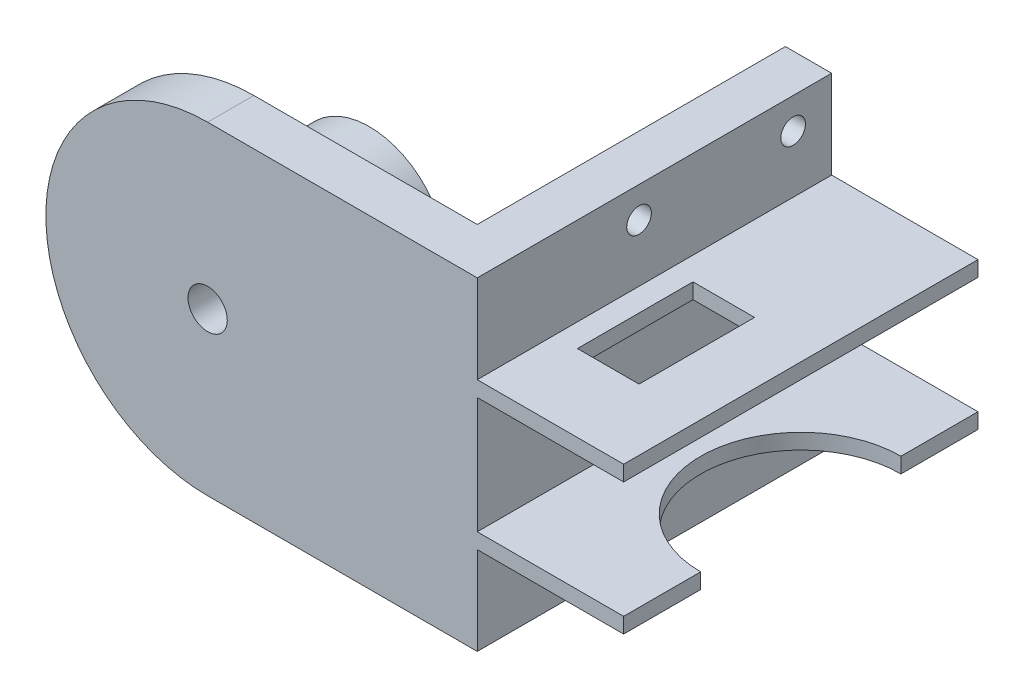
SolidWorks part; units mm, degrees
ref_plane "前视基准面" through (0, 0, 0) normal (0, 0, 1) x (1, 0, 0)
ref_plane "上视基准面" through (0, 0, 0) normal (0, 1, 0) x (1, 0, 0)
ref_plane "右视基准面" through (0, 0, 0) normal (1, 0, 0) x (0, 0, -1)
sketch "草图1" plane through (0, 0, 0) normal (0, 0, 1) x (1, 0, 0)
  circle A0 centre (-2.1417, 2.0638) radius 10
  circle A1 centre (-2.1417, 2.0638) radius 2.55
  dimension "D1" = 20
  dimension "D2" = 5.1
extrude "凸台-拉伸1" add sketch "草图1" along normal blind 15
sketch "草图2" plane through (0, 0, 15) normal (0, 0, 1) x (1, 0, 0)
  line L0 (-12.1417, 2.0638) -> (7.8583, 2.0638)
  circle A0 centre (-2.1417, 2.0638) radius 10 construction
ref_plane "基准面1" through (7.8583, 0, 0) normal (1, 0, 0) x (0, 0, -1)
sketch "草图3" plane through (7.8583, 0, 0) normal (1, 0, 0) x (0, 0, -1)
  line L0 (-15, 2.0638) -> (0, 2.0638) construction
  line L1 (-15, 12.0638) -> (-15, -7.9362) construction
  line L2 (0, -7.9362) -> (0, 12.0638) construction
  circle A0 centre (-7.5, 2.0638) radius 1.6
  dimension "D1" = 3.2
extrude "切除-拉伸1" cut sketch "草图3" against normal through all
sketch "草图5" plane through (0, 0, 15) normal (0, 0, 1) x (1, 0, 0)
  line L0 (7.8583, -8.25) -> (7.8583, 8.25) construction
  line L1 (-2.1417, 23.0638) -> (32.8583, 23.0638)
  line L3 (-2.1417, -18.9362) -> (32.8583, -18.9362)
  line L4 (32.8583, 23.0638) -> (32.8583, -18.9362)
  arc A0 (-2.1417, 23.0638) -> (-2.1417, -18.9362) centre (-2.1417, 2.0638) ccw
  dimension "D1" = 21
  dimension "D2" = 25
extrude "凸台-拉伸2" add sketch "草图5" along normal blind 6
sketch "草图6" plane through (0, 0, 15) normal (0, 0, -1) x (-1, 0, 0)
  line L0 (12.1417, 2.0638) -> (-7.8583, 2.0638) construction
  circle A0 centre (2.1417, 2.0638) radius 2.55
  circle A1 centre (2.1417, 2.0638) radius 2.55 construction
extrude "切除-拉伸2" cut sketch "草图6" against normal blind 10
sketch "草图7" plane through (32.8583, 0, 0) normal (1, 0, 0) x (0, 0, -1)
  line L0 (-21, -18.9362) -> (-15, -18.9362) construction
  line L1 (-15, 23.0638) -> (25, 23.0638)
  line L2 (-15, 23.0638) -> (-15, -18.9362)
  line L3 (-15, -18.9362) -> (25, -18.9362)
  line L4 (25, 23.0638) -> (25, -18.9362)
  dimension "D1" = 40
extrude "凸台-拉伸3" add sketch "草图7" against normal blind 6
sketch "草图8" plane through (32.8583, 0, 0) normal (1, 0, 0) x (0, 0, -1)
  line L0 (-21, 23.0638) -> (25, 23.0638) construction
  line L1 (0, 19.0638) -> (20, 19.0638) construction
  line L2 (0, 19.0638) -> (0, -14.9362) construction
  line L3 (0, -14.9362) -> (20, -14.9362) construction
  line L4 (20, 19.0638) -> (20, -14.9362) construction
  line L6 (25, -18.9362) -> (25, 23.0638) construction
  circle A0 centre (0, 19.0638) radius 1.6
  circle A1 centre (0, -14.9362) radius 1.6
  circle A2 centre (20, -14.9362) radius 1.6
  circle A3 centre (20, 19.0638) radius 1.6
  dimension "D5" = 3.2
  dimension "D1" = 4
  dimension "D2" = 34
  dimension "D3" = 5
  dimension "D4" = 20
extrude "切除-拉伸3" cut sketch "草图8" against normal blind 6
sketch "草图9" plane through (32.8583, 0, 0) normal (1, 0, 0) x (0, 0, -1)
  line L0 (-21, 2.0638) -> (25, 2.0638) construction
  line L1 (-21, -18.9362) -> (-21, 23.0638) construction
  line L2 (25, -18.9362) -> (25, 23.0638) construction
  line L4 (-21, 9.6138) -> (25, 9.6138)
  line L5 (-21, 9.6138) -> (-21, -5.4862) construction
  line L6 (-21, -5.4862) -> (25, -5.4862)
  line L7 (25, 9.6138) -> (25, -5.4862) construction
  line L8 (-21, -7.4862) -> (25, -7.4862)
  line L10 (-21, 11.6138) -> (25, 11.6138)
  line L11 (-21, 9.6138) -> (-21, 11.6138)
  line L12 (-21, -5.4862) -> (-21, -7.4862)
  line L13 (25, -5.4862) -> (25, -7.4862)
  line L14 (25, 11.6138) -> (25, 9.6138)
  line L15 (-23, 11.6138) -> (27, 11.6138) construction
  line L16 (-23, 11.6138) -> (-23, -7.4862) construction
  line L17 (-23, -7.4862) -> (27, -7.4862) construction
  line L18 (27, 11.6138) -> (27, -7.4862) construction
  line L20 (-21, 11.6138) -> (25, 11.6138)
  line L21 (-21, 11.6138) -> (-21, 9.6138)
  line L22 (-21, 9.6138) -> (25, 9.6138)
  line L23 (25, 11.6138) -> (25, 9.6138)
  line L24 (-21, -5.4862) -> (25, -5.4862)
  line L25 (-21, -5.4862) -> (-21, -7.4862)
  line L26 (-21, -7.4862) -> (25, -7.4862)
  line L27 (25, -5.4862) -> (25, -7.4862)
  line M20 (25, -18.9362) -> (25, 23.0638)
  line M22 (-21, 23.0638) -> (-21, -18.9362)
  dimension "D1" = 15.1
  dimension "D2" = 7.55
  dimension "D3" = 2
extrude "凸台-拉伸4" add sketch "草图9" along normal blind 19 contours L10 L4 M22 M20 | L8 L6 M22 M20
sketch "草图10" plane through (0, -7.4862, 0) normal (0, -1, 0) x (1, 0, 0)
  line L0 (51.8583, 21) -> (51.8583, -25) construction
  circle A0 centre (51.8583, -2) radius 13
  dimension "D1" = 26
extrude "切除-拉伸4" cut sketch "草图10" against normal blind 8
sketch "草图11" plane through (0, 11.6138, 0) normal (0, 1, 0) x (1, 0, 0)
  line L0 (51.8583, -21) -> (32.8583, -21) construction
  line L1 (35.8583, 4) -> (43.8583, 4)
  line L2 (35.8583, 4) -> (35.8583, -11)
  line L3 (35.8583, -11) -> (43.8583, -11)
  line L4 (43.8583, 4) -> (43.8583, -11)
  line L5 (32.8583, -21) -> (32.8583, 25) construction
  dimension "D1" = 25
  dimension "D2" = 15
  dimension "D3" = 8
  dimension "D4" = 3
extrude "切除-拉伸5" cut sketch "草图11" against normal blind 8
